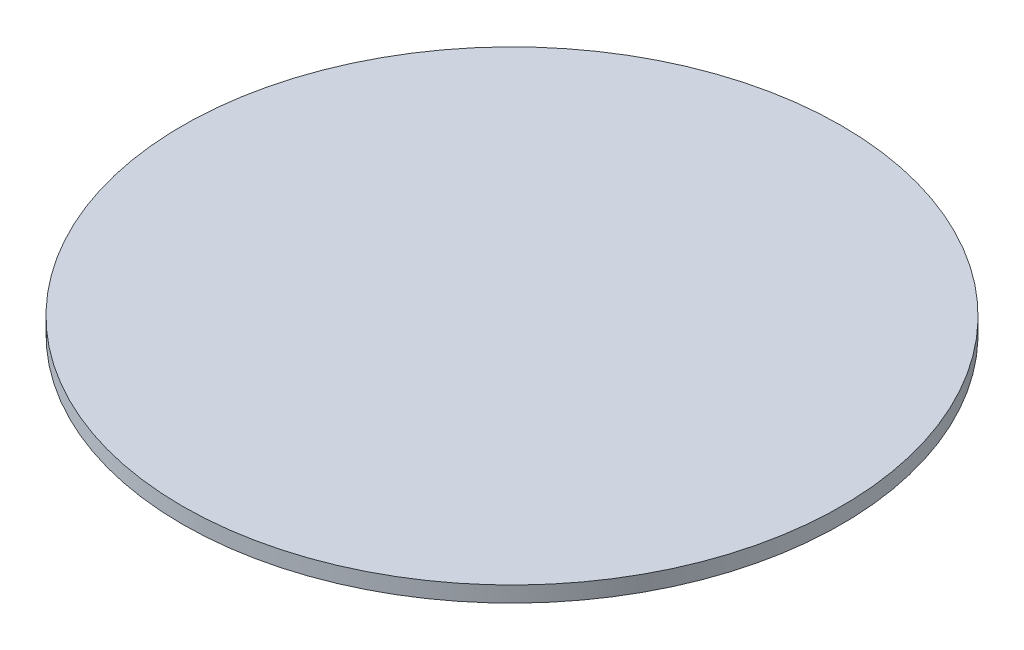
SolidWorks part; units mm, degrees
ref_plane "Front Plane" through (0, 0, 0) normal (0, 0, 1) x (1, 0, 0)
ref_plane "Top Plane" through (0, 0, 0) normal (0, 1, 0) x (1, 0, 0)
ref_plane "Right Plane" through (0, 0, 0) normal (1, 0, 0) x (0, 0, -1)
sketch "Sketch1" plane through (0, 0, 0) normal (0, 1, 0) x (1, 0, 0)
  circle A0 centre (0, 0) radius 105
  point P5 (0, -52.5)
  dimension "D2" = 210
extrude "Boss-Extrude4" add sketch "Sketch1" along normal blind 5
